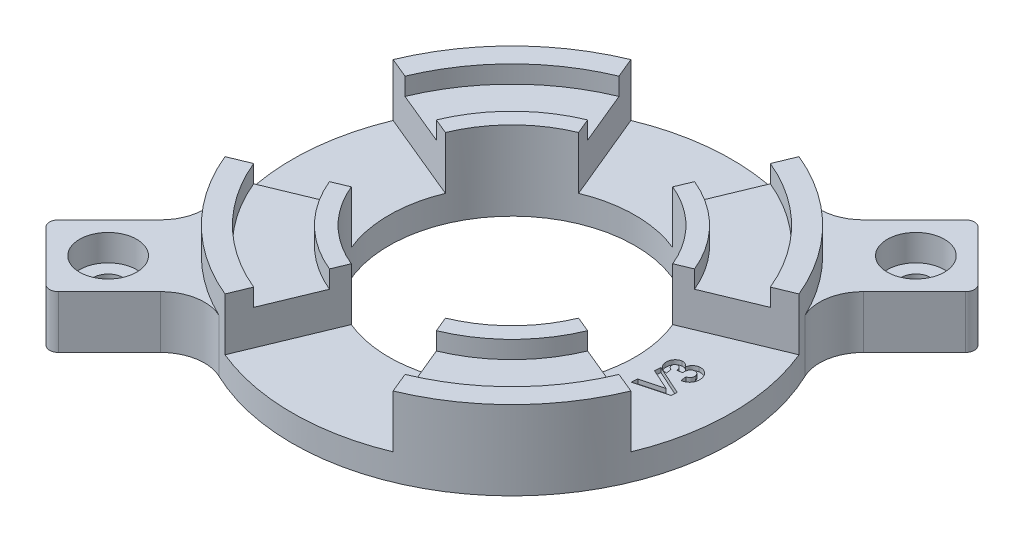
SolidWorks part; units mm, degrees
ref_plane "Front Plane" through (0, 0, 0) normal (0, 0, 1) x (1, 0, 0)
ref_plane "Top Plane" through (0, 0, 0) normal (0, 1, 0) x (1, 0, 0)
ref_plane "Right Plane" through (0, 0, 0) normal (1, 0, 0) x (0, 0, -1)
sketch "Sketch1" plane through (0, 0, 0) normal (0, 1, 0) x (1, 0, 0)
  circle A0 centre (0, 0) radius 25
  circle A1 centre (0, 0) radius 14
  dimension "D1" = 50
  dimension "D2" = 28
extrude "Boss-Extrude1" add sketch "Sketch1" along normal blind 7
sketch "Sketch3" plane through (0, 7, 0) normal (0, 1, 0) x (1, 0, 0)
  circle A0 centre (0, 0) radius 22.5
  circle A1 centre (0, 0) radius 25 construction
  circle A2 centre (0, 0) radius 25
  dimension "D1" = 45
extrude "Boss-Extrude2" add sketch "Sketch3" along normal blind 2
sketch "Sketch5" plane through (0, 7, 0) normal (0, 1, 0) x (1, 0, 0)
  circle A0 centre (0, 0) radius 14 construction
  circle A1 centre (0, 0) radius 14
  circle A2 centre (0, 0) radius 15.9
  dimension "D1" = 31.8
extrude "Boss-Extrude3" add sketch "Sketch5" along normal through all
sketch "Sketch4" plane through (0, 9, 0) normal (0, 1, 0) x (1, 0, 0)
  line L0 (0, 0) -> (-9.5671, 23.097)
  line L1 (0, 0) -> (0, 10.7947) construction
  line L2 (0, 0) -> (9.5671, 23.097)
  circle A0 centre (0, 0) radius 25 construction
  arc A1 (9.5671, 23.097) -> (-9.5671, 23.097) centre (0, 0) ccw
  dimension "D1" = 45
extrude "Cut-Extrude1" cut sketch "Sketch4" against normal blind 6
ref_axis "Axis1" through (0, 9, 0) along (0, -1, 0)
pattern_circular "CirPattern1" count 4 over 360 about axis through (0, 9, 0) along (0, -1, 0) of "Cut-Extrude1"
sketch "Sketch6" plane through (0, 0, 0) normal (0, -1, 0) x (1, 0, 0)
  line L0 (0, 0) -> (-15.9099, 15.9099) construction
  line L1 (-15.9099, 15.9099) -> (-17.6777, 17.6777) construction
  line L2 (-23.097, 9.5671) -> (-20.7873, 8.6104)
  line L3 (-8.6104, 20.7873) -> (-9.5671, 23.097)
  line L4 (-23.097, 9.5671) -> (-20.7873, 8.6104) construction
  line L5 (-8.6104, 20.7873) -> (-9.5671, 23.097) construction
  line L6 (23.097, -9.5671) -> (20.7873, -8.6104)
  line L7 (8.6104, -20.7873) -> (9.5671, -23.097)
  line L8 (23.097, -9.5671) -> (20.7873, -8.6104) construction
  line L9 (8.6104, -20.7873) -> (9.5671, -23.097) construction
  line L10 (-17.6777, 17.6777) -> (-1.6747, 1.6747) construction
  line L11 (-30.052, 22.981) -> (-22.981, 30.052)
  line L12 (-22.981, 30.052) -> (-13.785, 20.856)
  line L13 (-30.052, 22.981) -> (-20.856, 13.785)
  circle A0 centre (0, 0) radius 25 construction
  circle A1 centre (0, 0) radius 25
  circle A2 centre (0, 0) radius 25 construction
  arc A3 (-20.856, 13.785) -> (-13.785, 20.856) centre (0, 0) cw
  arc A4 (-9.5671, 23.097) -> (-23.097, 9.5671) centre (0, 0) ccw
  arc A5 (-8.6104, 20.7873) -> (-20.7873, 8.6104) centre (0, 0) ccw
  arc A6 (-9.5671, 23.097) -> (-23.097, 9.5671) centre (0, 0) ccw construction
  arc A7 (-8.6104, 20.7873) -> (-20.7873, 8.6104) centre (0, 0) ccw construction
  arc A8 (9.5671, -23.097) -> (23.097, -9.5671) centre (0, 0) ccw
  arc A9 (8.6104, -20.7873) -> (20.7873, -8.6104) centre (0, 0) ccw
  arc A10 (9.5671, -23.097) -> (23.097, -9.5671) centre (0, 0) ccw construction
  arc A11 (8.6104, -20.7873) -> (20.7873, -8.6104) centre (0, 0) ccw construction
  dimension "D4" = 10
  dimension "D5" = 12.5
  dimension "D1" = 0
  dimension "D2" = 0
  dimension "D3" = 0
extrude "Boss-Extrude4" add sketch "Sketch6" against normal blind 6
sketch "Sketch7" plane through (0, 6, 0) normal (0, 1, 0) x (1, 0, 0)
  line L0 (-26.5165, -26.5165) -> (-1.2144, -1.2144) construction
  line L1 (-22.981, -30.052) -> (-30.052, -22.981) construction
  line L2 (-13.785, -20.856) -> (-22.981, -30.052) construction
  point P6 (-22.981, -22.981)
  dimension "D1" = 5
hole_wizard "CBORE for M3 SHCS1" positions "Sketch7" profile "Sketch8" counterbore size "M3" standard "ANSI Metric" end condition up to next
sketch "Sketch8" plane through (-22.981, 6, 22.981) normal (1, 0, 0) x (0, 0, 1)
  line L0 (0, 0) -> (0, 6)
  line L1 (0, 6) -> (1.7, 6)
  line L3 (1.7, 6) -> (1.7, 3)
  line L4 (1.7, 3) -> (3.25, 3)
  line L5 (3.25, 3) -> (3.25, 0)
  line L7 (3.25, 0) -> (0, 0)
  line L11 (0, -6.35) -> (0, 107.95) construction
  dimension "Thru Hole Dia." = 3.4
  dimension "Thru Hole Depth" = 6
  dimension "C'Bore Dia." = 6.5
  dimension "C'Bore Depth" = 3
fillet "Fillet1" radius 5 2 edges at (-20.856, 3, 13.785) (-13.785, 3, 20.856)
ref_plane "Plane1" through (0, 0, 0) normal (-0.7071, 0, 0.7071) x (0.7071, 0, 0.7071)
mirror "Mirror1" about plane through (0, 0, 0) normal (-0.7071, 0, 0.7071) of "Fillet1", "CBORE for M3 SHCS1", "Boss-Extrude4"
fillet "Fillet2" radius 1 4 edges at (22.981, 3, -30.052) (30.052, 3, -22.981) (-22.981, 3, 30.052) (-30.052, 3, 22.981)
sketch "Sketch9" plane through (0, 3, 0) normal (0, 1, 0) x (1, 0, 0)
  line L0 (20.7873, 8.6104) -> (14.6897, 6.0847) construction
  line L1 (12.9343, -5.3576) -> (23.097, -9.5671) construction
  arc A0 (17.7385, 7.3475) -> (18.0157, -7.4623) centre (5.9986, -0.2797) cw construction
  arc A1 (12.9343, -5.3576) -> (12.9343, 5.3576) centre (0, 0) ccw construction
  text T0 "<b>V3</b>" font "Century Gothic" height 3.5
extrude "Cut-Extrude2" cut sketch "Sketch9" against normal blind 0.5
